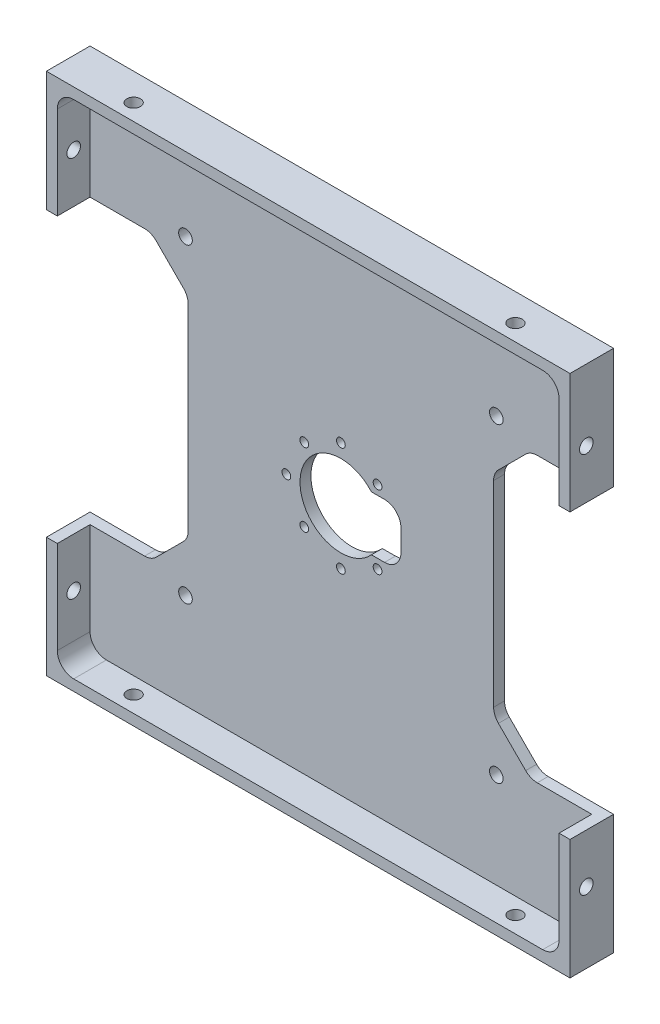
SolidWorks part; units mm, degrees
material "6061-T6 (SS)"
ref_plane "Front" through (0, 0, 0) normal (0, 0, 1) x (1, 0, 0)
ref_plane "Top" through (0, 0, 0) normal (0, 1, 0) x (1, 0, 0)
ref_plane "Right" through (0, 0, 0) normal (1, 0, 0) x (0, 0, -1)
sketch "Sketch1" plane through (0, 0, 0) normal (0, 0, 1) x (1, 0, 0)
  line L1 (-48, -48) -> (48, -48)
  line L2 (-48, -48) -> (-48, 48)
  line L3 (-48, 48) -> (48, 48)
  line L4 (48, -48) -> (48, 48)
  line L5 (-48, -48) -> (48, 48) construction
  line L6 (-48, 48) -> (48, -48) construction
  point P0 (0, 0)
  dimension "D1" = 96
  dimension "D2" = 96
extrude "Boss-Extrude1" add sketch "Sketch1" along normal blind 8
sketch "Sketch2" plane through (0, 0, 8) normal (0, 0, 1) x (1, 0, 0)
  line L1 (46, -46) -> (-46, -46)
  line L2 (46, -46) -> (46, 46)
  line L3 (46, 46) -> (-46, 46)
  line L4 (-46, -46) -> (-46, 46)
  line L5 (46, -46) -> (-46, 46) construction
  line L6 (46, 46) -> (-46, -46) construction
  point P0 (0, 0)
  dimension "D1" = 92
  dimension "D2" = 92
extrude "Component Platform" cut sketch "Sketch2" against normal blind 6
sketch "Sketch3" plane through (0, 0, 2) normal (0, 0, 1) x (1, 0, 0)
  line L1 (-33.8787, -25.1213) -> (-28.8787, -20.1213)
  line L2 (-33.8787, 25.1213) -> (-28.8787, 20.1213)
  line L3 (-28, -18) -> (-28, 18)
  line L4 (-48, -26) -> (-36, -26)
  line L7 (-48, 48) -> (-48, -48) construction
  line L8 (0, -56.7987) -> (0, 73.4321) construction
  line L9 (46, -46) -> (-57.8147, 57.8147) construction
  line L18 (46, 46) -> (-68.5705, -68.5705) construction
  line L23 (-48, 26) -> (-36, 26)
  line L26 (-48, -26) -> (-48, 26)
  line L28 (-48, -48) -> (48, -48) construction
  line L29 (48, -26) -> (48, 26)
  line L30 (48, 26) -> (36, 26)
  line L31 (33.8787, 25.1213) -> (28.8787, 20.1213)
  line L32 (28, -18) -> (28, 18)
  line L33 (33.8787, -25.1213) -> (28.8787, -20.1213)
  line L34 (48, -26) -> (36, -26)
  arc A3 (-28.8787, -20.1213) -> (-28, -18) centre (-31, -18) ccw
  arc A4 (-28.8787, 20.1213) -> (-28, 18) centre (-31, 18) cw
  arc A13 (-33.8787, -25.1213) -> (-36, -26) centre (-36, -23) cw
  arc A15 (-33.8787, 25.1213) -> (-36, 26) centre (-36, 23) ccw
  arc A17 (33.8787, 25.1213) -> (36, 26) centre (36, 23) cw
  arc A18 (28.8787, 20.1213) -> (28, 18) centre (31, 18) ccw
  arc A19 (28.8787, -20.1213) -> (28, -18) centre (31, -18) cw
  arc A20 (33.8787, -25.1213) -> (36, -26) centre (36, -23) ccw
  point P0 (-48, 0)
  point P37 (-48, 0)
  dimension "D2" = 3
  dimension "D3" = 3
  dimension "D4" = 20
  dimension "D6" = 3
  dimension "D7" = 3
  dimension "D8" = 135
  dimension "D5" = 52
  dimension "D9" = 135
  dimension "D10" = 12
  dimension "D11" = 12
  dimension "D12" = 48
extrude "Cable Slots" cut sketch "Sketch3" against normal mid plane 12
sketch "Sketch4" plane through (0, 0, 2) normal (0, 0, 1) x (1, 0, 0)
  circle A0 centre (0, 0) radius 7.5
  dimension "D1" = 15
extrude "Center Mass Cut" cut sketch "Sketch4" against normal blind 6
ref_plane "Center Y-Plane" through (0, 0, 0) normal (1, 0, 0) x (0, 0, -1)
ref_plane "Center X-Plane" through (0, 0, 0) normal (0, -1, 0) x (-1, 0, 0)
fillet "Inner Corner Fillets" radius 3 4 edges at (46, -46, 5) (-46, -46, 5) (46, 46, 5) (-46, 46, 5)
sketch "Sketch10" plane through (0, 0, 2) normal (0, 0, 1) x (1, 0, 0)
  line L1 (0, -5) -> (11, -5)
  line L2 (11, -5) -> (11, 5)
  line L3 (11, 5) -> (0, 5)
  line L5 (0, -5) -> (0, 5)
  point P3 (0, 0)
  dimension "D1" = 10
  dimension "D3" = 11
extrude "Motor Cutout" cut sketch "Sketch10" against normal blind 2
fillet "Fillet1" radius 3 2 edges at (11, 5, 1) (11, -5, 1)
sketch "Sketch11" plane through (0, 0, 2) normal (0, 0, 1) x (1, 0, 0)
  line L0 (0, 0) -> (0, 23.9217) construction
  line L1 (0, 0) -> (0, -24.7081) construction
  line L2 (0, 0) -> (-16.3847, 0) construction
  line L3 (0, 0) -> (16.7779, 0) construction
  circle A0 centre (6.72, 6.72) radius 1.05
  circle A1 centre (-6.72, 6.72) radius 1.05
  circle A2 centre (-6.72, -6.72) radius 1.05
  circle A3 centre (6.72, -6.72) radius 1.05
  circle A4 centre (0, 10) radius 1.05
  circle A5 centre (-10, 0) radius 1.05
  circle A6 centre (0, -10) radius 1.05
  dimension "D9" = 2.1
  dimension "D1" = 6.72
  dimension "D2" = 6.72
  dimension "D3" = 6.72
  dimension "D4" = 6.72
  dimension "D5" = 6.72
  dimension "D6" = 6.72
  dimension "D7" = 6.72
  dimension "D8" = 6.72
  dimension "D10" = 10
  dimension "D11" = 10
  dimension "D12" = 10
sketch "Sketch12" plane through (48, 0, 0) normal (1, 0, 0) x (0, 0, -1)
  line L0 (-5, -48) -> (-5, 48) construction
  line L1 (-8, -48) -> (0, -48) construction
  line L2 (-8, 48) -> (0, 48) construction
  line L3 (-8, -48) -> (-8, -26) construction
  dimension "D1" = 3
hole_wizard "M3x0.5 Tapped Hole1" positions "Sketch13" profile "Sketch14" tap size "M3x0.5" standard "ANSI Metric"
sketch "Sketch13" plane through (48, 0, 0) normal (1, 0, 0) x (0, 0, -1)
  line L0 (-5, -48) -> (-5, 48) construction
  point P0 (-5, -35)
  point P4 (-5, 35)
  dimension "D1" = 70
  dimension "D2" = 35
sketch "Sketch14" plane through (48, -35, 5) normal (0, 1, 0) x (0, 0, -1)
  line L0 (0, 0) -> (0, 8.2511)
  line L1 (0, 8.2511) -> (1.25, 7.5)
  line L2 (1.25, 7.5) -> (1.25, 0)
  line L5 (1.25, 0) -> (0, 0)
  line L10 (0, 8.2511) -> (-1.25, 7.5) construction
  line L11 (0, -6.35) -> (0, 107.95) construction
  dimension "Tap Drill Dia." = 2.5
  dimension "Tap Drill Depth" = 7.5
  dimension "Drill Angle" = 118
sketch "Sketch15" plane through (0, 48, 0) normal (0, 1, 0) x (1, 0, 0)
  line L0 (-48, -5) -> (48, -5) construction
  line L1 (-48, -8) -> (-48, 0) construction
  line L2 (48, -8) -> (48, 0) construction
  line L3 (48, -8) -> (-48, -8) construction
  dimension "D1" = 3
hole_wizard "M3x0.5 Tapped Hole2" positions "Sketch16" profile "Sketch17" tap size "M3x0.5" standard "ANSI Metric"
sketch "Sketch16" plane through (0, 48, 0) normal (0, 1, 0) x (1, 0, 0)
  line L0 (-48, -5) -> (48, -5) construction
  point P0 (35, -5)
  point P4 (-35, -5)
  dimension "D1" = 70
  dimension "D2" = 35
sketch "Sketch17" plane through (35, 48, 5) normal (1, 0, 0) x (0, 0, 1)
  line L0 (0, 0) -> (0, 8.2511)
  line L1 (0, 8.2511) -> (1.25, 7.5)
  line L2 (1.25, 7.5) -> (1.25, 0)
  line L5 (1.25, 0) -> (0, 0)
  line L10 (0, 8.2511) -> (-1.25, 7.5) construction
  line L11 (0, -6.35) -> (0, 107.95) construction
  dimension "Tap Drill Dia." = 2.5
  dimension "Tap Drill Depth" = 7.5
  dimension "Drill Angle" = 118
mirror "Mirror1" about plane through (0, 0, 0) normal (1, 0, 0) of "M3x0.5 Tapped Hole1"
mirror "Mirror2" about plane through (0, 0, 0) normal (0, -1, 0) of "M3x0.5 Tapped Hole2"
sketch "Sketch18" plane through (0, 0, 2) normal (0, 0, 1) x (1, 0, 0)
  line L0 (0, -46) -> (0, 46) construction
  line L1 (-43, -46) -> (43, -46) construction
  line L2 (43, 46) -> (-43, 46) construction
  line L6 (46, -28.5) -> (-46, -28.5) construction
  line L7 (46, -43) -> (46, -26) construction
  line L8 (-46, -26) -> (-46, -43) construction
  line L9 (-28.5, -46) -> (-28.5, 46) construction
  line L10 (-43, -46) -> (43, -46) construction
  dimension "D1" = 17.5
  dimension "D2" = 28.5
hole_wizard "M3x0.5 Tapped Hole3" positions "Sketch19" profile "Sketch20" tap size "M3x0.5" standard "ANSI Metric"
sketch "Sketch19" plane through (0, 0, 2) normal (0, 0, 1) x (1, 0, 0)
  line L0 (46, -28.5) -> (-46, -28.5) construction
  line L1 (-28.5, -46) -> (-28.5, 46) construction
  point P0 (-28.5, -28.5)
sketch "Sketch20" plane through (-28.5, -28.5, 2) normal (1, 0, 0) x (0, -1, 0)
  line L0 (0, 0) -> (0, 8.2511)
  line L1 (0, 8.2511) -> (1.25, 7.5)
  line L2 (1.25, 7.5) -> (1.25, 0)
  line L5 (1.25, 0) -> (0, 0)
  line L10 (0, 8.2511) -> (-1.25, 7.5) construction
  line L11 (0, -6.35) -> (0, 107.95) construction
  dimension "Tap Drill Dia." = 2.5
  dimension "Tap Drill Depth" = 7.5
  dimension "Drill Angle" = 118
cosmetic thread "Hole Thread1" parameters "D1"=2, "D2"=3
mirror "Mirror3" about plane through (0, 0, 0) normal (1, 0, 0) of "M3x0.5 Tapped Hole3"
mirror "Mirror4" about plane through (0, 0, 0) normal (0, 1, 0) of "M3x0.5 Tapped Hole3", "Mirror3"
hole_wizard "M2x0.4 Tapped Hole1" positions "Sketch23" profile "Sketch24" tap size "M2x0.4" standard "ANSI Metric"
sketch "Sketch23" plane through (0, 0, 2) normal (0, 0, 1) x (1, 0, 0)
  point P0 (6.72, -6.72)
  point P3 (0, -10)
  point P6 (-6.72, -6.72)
  point P9 (-10, 0)
  point P12 (-6.72, 6.72)
  point P15 (0, 10)
  point P18 (6.72, 6.72)
sketch "Sketch24" plane through (6.72, -6.72, 2) normal (1, 0, 0) x (0, -1, 0)
  line L0 (0, 0) -> (0, 5.6807)
  line L1 (0, 5.6807) -> (0.8, 5.2)
  line L2 (0.8, 5.2) -> (0.8, 0)
  line L5 (0.8, 0) -> (0, 0)
  line L10 (0, 5.6807) -> (-0.8, 5.2) construction
  line L11 (0, -6.35) -> (0, 107.95) construction
  dimension "Tap Drill Dia." = 1.6
  dimension "Tap Drill Depth" = 5.2
  dimension "Drill Angle" = 118
cosmetic thread "Hole Thread2" parameters "D1"=2, "D2"=2
cosmetic thread "Hole Thread3" parameters "D1"=2, "D2"=2
cosmetic thread "Hole Thread4" parameters "D1"=2, "D2"=2
cosmetic thread "Hole Thread5" parameters "D1"=2, "D2"=2
cosmetic thread "Hole Thread6" parameters "D1"=2, "D2"=2
cosmetic thread "Hole Thread7" parameters "D1"=2, "D2"=2
cosmetic thread "Hole Thread8" parameters "D1"=2, "D2"=2
